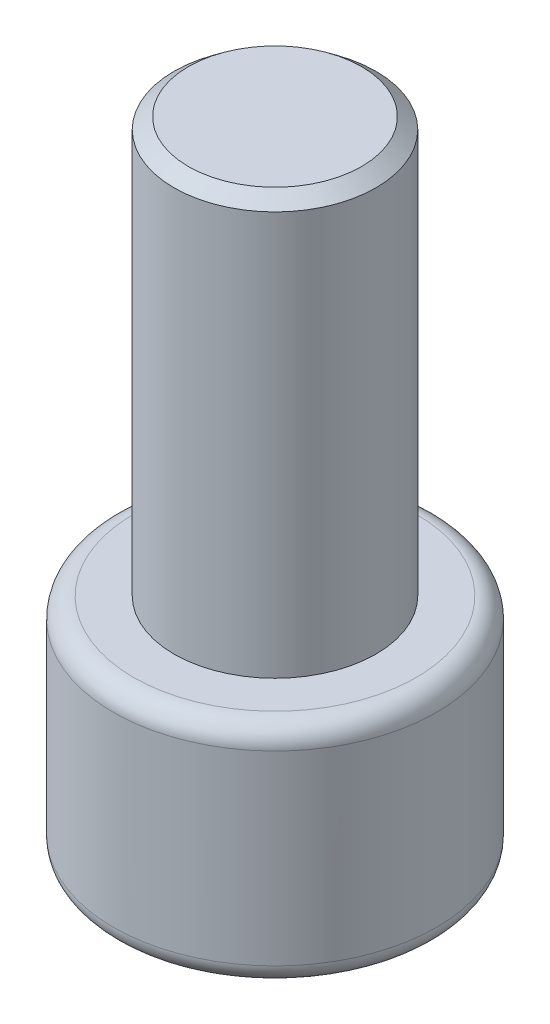
SolidWorks part; units mm, degrees
material "AISI 1020"
ref_plane "Alzado" through (0, 0, 0) normal (0, 0, 1) x (1, 0, 0)
ref_plane "Planta" through (0, 0, 0) normal (0, 1, 0) x (1, 0, 0)
ref_plane "Vista lateral" through (0, 0, 0) normal (1, 0, 0) x (0, 0, -1)
sketch "Croquis1" plane through (0, 0, 0) normal (0, 0, 1) x (1, 0, 0)
  line L0 (0, 0) -> (0, 85.9498) construction
  line L1 (-5, 31.2164) -> (-5, 11.2164)
  line L2 (-5, 11.2164) -> (-15.9235, 2.682) construction
  line L3 (-15, 0) -> (0, 0) construction
  line L4 (-15, 0) -> (-15, 5.5806) construction
  line L5 (-15.9235, 2.682) -> (-8, -7.4596) construction
  line L6 (-5, 31.2164) -> (-4.2883, 31.7724)
  line L7 (-4.2883, 31.7724) -> (0, 31.7724)
  line L8 (-5, 31.2164) -> (1.4006, 31.2164) construction
  line L9 (0, 0) -> (0, 31.7724)
  line L10 (-5, 11.2164) -> (-8, 11.2164)
  line L11 (-8, 11.2164) -> (-8, 0)
  line L12 (-8, 0) -> (0, 0)
  arc A0 (-15.9235, 2.682) -> (-15, 0) centre (-15, 1.5) ccw construction
  point P10 (-15, 1.5)
  dimension "D2" = 1.5
  dimension "D5" = 8
  dimension "D1" = 38
  dimension "D3" = 15
  dimension "D4" = 5
  dimension "D6" = 20
  dimension "D7" = 38
  dimension "D8" = 4.2883
revolve "Revolución2" add sketch "Croquis1" angle 360 about L0
sketch "Croquis2" plane through (0, 0, 0) normal (0, -1, 0) x (1, 0, 0)
  line L1 (0, 5.1962) -> (-4.5, 2.5981)
  line L2 (-4.5, 2.5981) -> (-4.5, -2.5981)
  line L3 (-4.5, -2.5981) -> (0, -5.1962)
  line L4 (0, -5.1962) -> (4.5, -2.5981)
  line L5 (4.5, -2.5981) -> (4.5, 2.5981)
  line L6 (4.5, 2.5981) -> (0, 5.1962)
  circle A0 centre (0, 0) radius 4.5 construction
  dimension "D1" = 9
extrude "Cortar-Extruir1" cut sketch "Croquis2" against normal blind 7
fillet "Redondeo1" radius 1 2 edges at (0, 0, -8) (0, 11.2164, -8)
